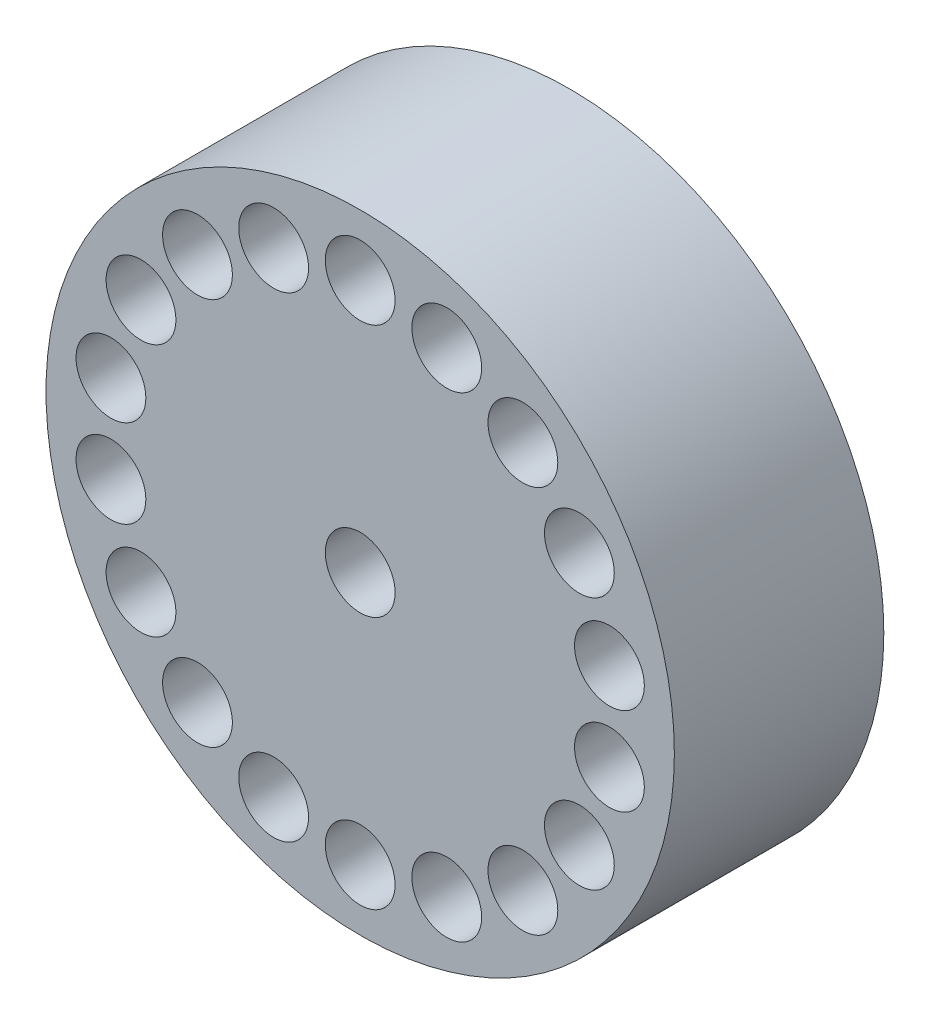
SolidWorks part; units mm, degrees
ref_plane "Płaszczyzna przednia" through (0, 0, 0) normal (0, 0, 1) x (1, 0, 0)
ref_plane "Płaszczyzna górna" through (0, 0, 0) normal (0, 1, 0) x (1, 0, 0)
ref_plane "Płaszczyzna prawa" through (0, 0, 0) normal (1, 0, 0) x (0, 0, -1)
sketch "Szkic1" plane through (0, 0, 0) normal (0, 0, 1) x (1, 0, 0)
  circle A0 centre (0, 0) radius 4.5
  circle A1 centre (0, 0) radius 0.5
extrude "Dodanie-wyciągnięcie1" add sketch "Szkic1" along normal blind 3
sketch "Szkic2" plane through (0, 0, 3) normal (0, 0, 1) x (1, 0, 0)
  circle A0 centre (0, 3.625) radius 0.5
  circle A1 centre (1.2398, 3.4064) radius 0.5
  circle A2 centre (2.3301, 2.7769) radius 0.5
  circle A3 centre (3.1393, 1.8125) radius 0.5
  circle A4 centre (3.5699, 0.6295) radius 0.5
  circle A5 centre (3.5699, -0.6295) radius 0.5
  circle A6 centre (3.1393, -1.8125) radius 0.5
  circle A7 centre (2.3301, -2.7769) radius 0.5
  circle A8 centre (1.2398, -3.4064) radius 0.5
  circle A9 centre (0, -3.625) radius 0.5
  circle A10 centre (-1.2398, -3.4064) radius 0.5
  circle A11 centre (-2.3301, -2.7769) radius 0.5
  circle A12 centre (-3.1393, -1.8125) radius 0.5
  circle A13 centre (-3.5699, -0.6295) radius 0.5
  circle A14 centre (-3.5699, 0.6295) radius 0.5
  circle A15 centre (-3.1393, 1.8125) radius 0.5
  circle A16 centre (-2.3301, 2.7769) radius 0.5
  circle A17 centre (-1.2398, 3.4064) radius 0.5
  point P40 (0, 0)
  dimension "D1" = 1
  dimension "D2" = 3.625
  dimension "D3" = 18
extrude "Wytnij-wyciągnięcie2" cut sketch "Szkic2" against normal blind 1
